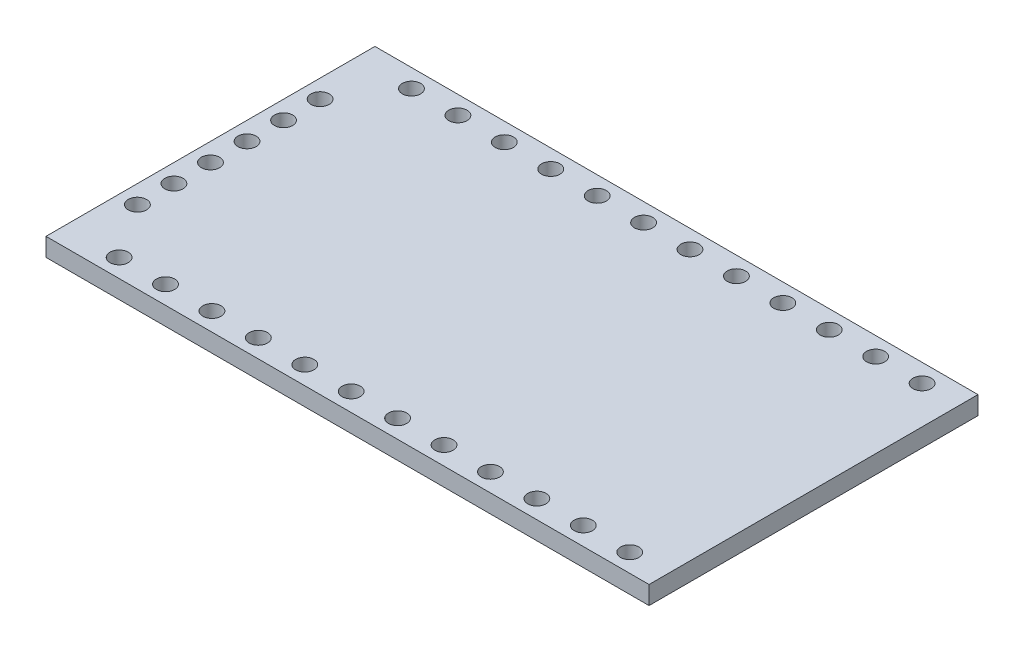
SolidWorks part; units mm, degrees
ref_plane "Alzado" through (0, 0, 0) normal (0, 0, 1) x (1, 0, 0)
ref_plane "Planta" through (0, 0, 0) normal (0, 1, 0) x (1, 0, 0)
ref_plane "Vista lateral" through (0, 0, 0) normal (1, 0, 0) x (0, 0, -1)
sketch "Croquis1" plane through (0, 0, 0) normal (0, 1, 0) x (1, 0, 0)
  line L0 (-29.7075, 0) -> (13.7236, 0) construction
  line L1 (-23.6385, -9) -> (-23.6385, 9)
  line L2 (-23.6385, 9) -> (9.3615, 9)
  line L3 (9.3615, 9) -> (9.3615, -9)
  line L4 (-23.6385, -9) -> (9.3615, -9)
  circle A0 centre (-22.6385, 1) radius 0.5
  circle A1 centre (-22.6385, 3) radius 0.5
  circle A2 centre (-22.6385, 5) radius 0.5
  circle A3 centre (-20.6385, 8) radius 0.5
  circle A4 centre (-18.0985, 8) radius 0.5
  circle A5 centre (-15.5585, 8) radius 0.5
  circle A6 centre (-13.0185, 8) radius 0.5
  circle A7 centre (-10.4785, 8) radius 0.5
  circle A8 centre (-7.9385, 8) radius 0.5
  circle A9 centre (-5.3985, 8) radius 0.5
  circle A10 centre (-2.8585, 8) radius 0.5
  circle A11 centre (-0.3185, 8) radius 0.5
  circle A12 centre (2.2215, 8) radius 0.5
  circle A13 centre (4.7615, 8) radius 0.5
  circle A14 centre (7.3015, 8) radius 0.5
  circle A15 centre (7.3015, -8) radius 0.5
  circle A16 centre (4.7615, -8) radius 0.5
  circle A17 centre (2.2215, -8) radius 0.5
  circle A18 centre (-0.3185, -8) radius 0.5
  circle A19 centre (-2.8585, -8) radius 0.5
  circle A20 centre (-5.3985, -8) radius 0.5
  circle A21 centre (-7.9385, -8) radius 0.5
  circle A22 centre (-10.4785, -8) radius 0.5
  circle A23 centre (-13.0185, -8) radius 0.5
  circle A24 centre (-15.5585, -8) radius 0.5
  circle A25 centre (-18.0985, -8) radius 0.5
  circle A26 centre (-20.6385, -8) radius 0.5
  circle A27 centre (-22.6385, -5) radius 0.5
  circle A28 centre (-22.6385, -3) radius 0.5
  circle A29 centre (-22.6385, -1) radius 0.5
  point P68 (9.3615, 0)
  point P69 (-23.6385, 0)
  dimension "D3" = 1
  dimension "D4" = 1
  dimension "D5" = 1
  dimension "D8" = 1
  dimension "D9" = 1
  dimension "D1" = 33
  dimension "D2" = 9
  dimension "D7" = 2
  dimension "D6" = 3
  dimension "D10" = 12
extrude "Saliente-Extruir1" add sketch "Croquis1" along normal blind 1
